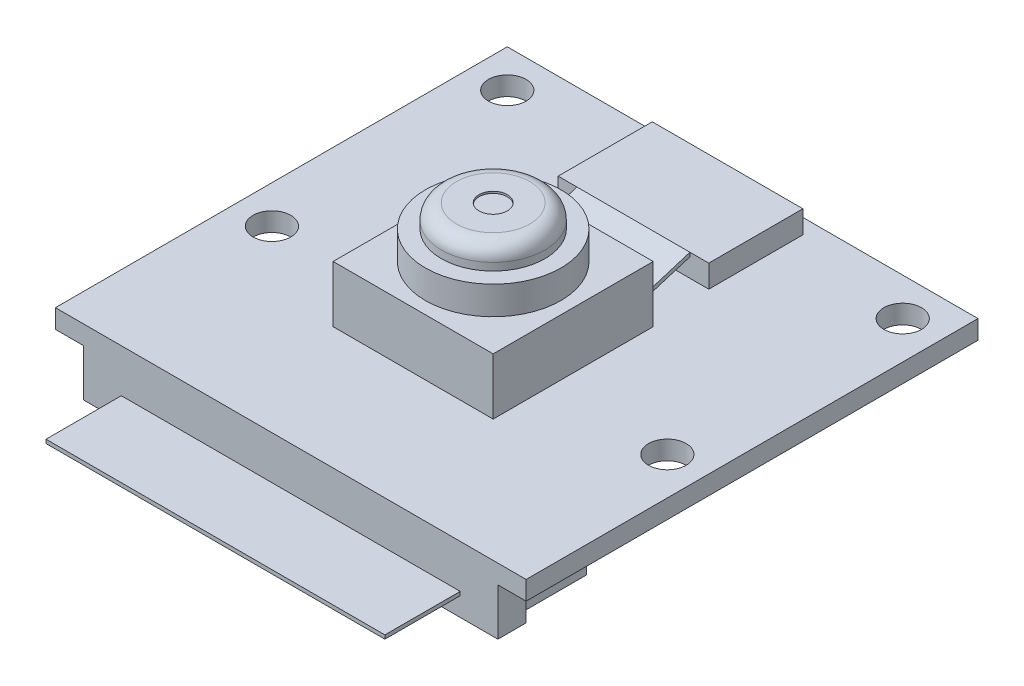
SolidWorks part; units mm, degrees
ref_plane "前视基准面" through (0, 0, 0) normal (0, 0, 1) x (1, 0, 0)
ref_plane "上视基准面" through (0, 0, 0) normal (0, 1, 0) x (1, 0, 0)
ref_plane "右视基准面" through (0, 0, 0) normal (1, 0, 0) x (0, 0, -1)
sketch "草图1" plane through (0, 0, 0) normal (0, 1, 0) x (1, 0, 0)
  line L1 (12.5, -12) -> (-12.5, -12)
  line L2 (12.5, -12) -> (12.5, 12)
  line L3 (12.5, 12) -> (-12.5, 12)
  line L4 (-12.5, -12) -> (-12.5, 12)
  line L5 (12.5, -12) -> (-12.5, 12) construction
  line L6 (12.5, 12) -> (-12.5, -12) construction
  point P0 (0, 0)
  dimension "D1" = 24
  dimension "D2" = 25
extrude "凸台-拉伸1" add sketch "草图1" along normal blind 1
sketch "草图2" plane through (0, 1, 0) normal (0, 1, 0) x (1, 0, 0)
  line L0 (0, 12) -> (0, -12) construction
  line L1 (12.5, 12) -> (-12.5, 12) construction
  line L2 (-12.5, -12) -> (12.5, -12) construction
  line L3 (-12.5, 0) -> (12.5, 0) construction
  line L4 (-12.5, 12) -> (-12.5, -12) construction
  line L5 (12.5, -12) -> (12.5, 12) construction
  circle A0 centre (-10.5, 10) radius 1
  circle A1 centre (-10.5, -2.5) radius 1
  circle A2 centre (10.5, -2.5) radius 1
  circle A3 centre (10.5, 10) radius 1
  dimension "D3" = 2
  dimension "D4" = 2
  dimension "D1" = 2
  dimension "D2" = 2
extrude "切除-拉伸1" cut sketch "草图2" against normal up to next
sketch "草图3" plane through (0, 1, 0) normal (0, 1, 0) x (1, 0, 0)
  line L0 (0, 12) -> (0, -12) construction
  line L1 (12.5, 12) -> (-12.5, 12) construction
  line L2 (-12.5, -12) -> (12.5, -12) construction
  line L4 (4.25, -5.5) -> (-4.25, -5.5)
  line L5 (4.25, -5.5) -> (4.25, 3)
  line L6 (4.25, 3) -> (-4.25, 3)
  line L7 (-4.25, -5.5) -> (-4.25, 3)
  line L8 (4.25, -5.5) -> (-4.25, 3) construction
  line L9 (4.25, 3) -> (-4.25, -5.5) construction
  point P6 (0, -1.25)
  dimension "D1" = 8.5
  dimension "D2" = 8.5
  dimension "D3" = 6.5
extrude "凸台-拉伸2" add sketch "草图3" along normal blind 3
sketch "草图4" plane through (0, 4, 0) normal (0, 1, 0) x (1, 0, 0)
  line L0 (-4.25, -1.25) -> (4.25, -1.25) construction
  line L1 (-4.25, 3) -> (-4.25, -5.5) construction
  line L2 (4.25, -5.5) -> (4.25, 3) construction
  line L3 (0, 3) -> (0, -5.5) construction
  line L4 (4.25, 3) -> (-4.25, 3) construction
  line L5 (-4.25, -5.5) -> (4.25, -5.5) construction
  circle A0 centre (0, -1.25) radius 3.6
  dimension "D1" = 7.2
extrude "凸台-拉伸3" add sketch "草图4" along normal blind 1.5
sketch "草图5" plane through (0, 5.5, 0) normal (0, 1, 0) x (1, 0, 0)
  line L0 (-4.25, -1.25) -> (4.25, -1.25) construction
  line L1 (-4.25, 3) -> (-4.25, -5.5) construction
  line L2 (4.25, -5.5) -> (4.25, 3) construction
  line L3 (0, 3) -> (0, -5.5) construction
  line L4 (4.25, 3) -> (-4.25, 3) construction
  line L5 (-4.25, -5.5) -> (4.25, -5.5) construction
  circle A0 centre (0, -1.25) radius 2.75
  dimension "D1" = 5.5
extrude "凸台-拉伸4" add sketch "草图5" along normal blind 1.2
fillet "圆角1" radius 0.8 1 edges at (0, 6.7, 4)
sketch "草图6" plane through (0, 6.7, 0) normal (0, 1, 0) x (1, 0, 0)
  line L4 (-4.25, 3) -> (-4.25, -5.5)
  line L5 (-4.25, -5.5) -> (4.25, -5.5)
  line L6 (4.25, -5.5) -> (4.25, 3)
  line L7 (4.25, 3) -> (-4.25, 3)
  line L8 (-4.25, 3) -> (-4.25, -5.5) construction
  line L9 (-4.25, -5.5) -> (4.25, -5.5) construction
  line L10 (4.25, -5.5) -> (4.25, 3) construction
  line L11 (4.25, 3) -> (-4.25, 3) construction
  circle A0 centre (0, -1.25) radius 0.75
  dimension "D2" = 1.5
  dimension "D1" = 0
extrude "切除-拉伸2" cut sketch "草图6" against normal blind 0.1
sketch "草图7" plane through (0, 1, 0) normal (0, 1, 0) x (1, 0, 0)
  line L1 (4, 6.2) -> (-4, 6.2)
  line L2 (4, 6.2) -> (4, 11.2)
  line L3 (4, 11.2) -> (-4, 11.2)
  line L4 (-4, 6.2) -> (-4, 11.2)
  line L5 (4, 6.2) -> (-4, 11.2) construction
  line L6 (4, 11.2) -> (-4, 6.2) construction
  line L10 (-12.5, 12) -> (-12.5, -12)
  line L11 (-12.5, -12) -> (12.5, -12)
  line L12 (12.5, -12) -> (12.5, 12)
  line L13 (12.5, 12) -> (-12.5, 12)
  line L14 (-12.5, 12) -> (-12.5, -12) construction
  line L15 (-12.5, -12) -> (12.5, -12) construction
  line L16 (12.5, -12) -> (12.5, 12) construction
  line L17 (12.5, 12) -> (-12.5, 12) construction
  point P0 (0, 8.7)
  point P7 (0, 0)
  point P9 (0, 12)
  dimension "D1" = 5
  dimension "D2" = 8
  dimension "D4" = 0.8
  dimension "D3" = 0
extrude "凸台-拉伸5" add sketch "草图7" along normal blind 1.2
sketch "草图8" plane through (0, 0, 0) normal (1, 0, 0) x (0, 0, -1)
  line L0 (3, 1.2094) -> (6.2, 2.2)
  line L1 (3, 4) -> (3, 1) construction
  line L2 (6.2, 2.2) -> (6.2, 1.9906)
  line L3 (6.2, 2.2) -> (6.2, 1) construction
  line L4 (6.2, 1.9906) -> (3, 1)
  line L5 (3, 1) -> (3, 1.2094)
  dimension "D1" = 0.2
extrude "凸台-拉伸6" add sketch "草图8" along normal blind 3 and the other way blind 3 separate body
sketch "草图9" plane through (0, 0, 0) normal (0, -1, 0) x (1, 0, 0)
  line L0 (-12.5, 12) -> (12.5, 12) construction
  line L1 (11, 10.5) -> (-11, 10.5)
  line L2 (11, 10.5) -> (11, 12)
  line L3 (11, 12) -> (-11, 12)
  line L4 (-11, 10.5) -> (-11, 12)
  line L5 (11, 10.5) -> (-11, 12) construction
  line L6 (11, 12) -> (-11, 10.5) construction
  point P0 (0, 11.25)
  point P7 (0, 0)
  dimension "D1" = 1.5
  dimension "D2" = 22
extrude "凸台-拉伸7" add sketch "草图9" along normal blind 2.5
sketch "草图12" plane through (0, 0, 0) normal (0, -1, 0) x (1, 0, 0)
  line L0 (-12.5, -12) -> (-12.5, 12) construction
  line L1 (-10.5, 10.5) -> (10.5, 10.5)
  line L2 (-10.5, 10.5) -> (-10.5, 6.8)
  line L3 (-10.5, 6.8) -> (10.5, 6.8)
  line L4 (10.5, 10.5) -> (10.5, 6.8)
  point P5 (0, 0)
  dimension "D1" = 21
  dimension "D2" = 3.7
  dimension "D3" = 2
extrude "凸台-拉伸8" add sketch "草图12" along normal blind 2.4
sketch "草图13" plane through (0, 0, 0) normal (1, 0, 0) x (0, 0, -1)
  line L0 (-6.8, -1.0088) -> (-6.1774, -0.1907)
  line L1 (-6.8, -2.4) -> (-6.8, 0) construction
  line L2 (-6.1774, -0.1907) -> (-4.9878, 0)
  line L3 (-12, 0) -> (12, 0) construction
  line L4 (-4.9878, 0) -> (-4.3247, 0)
  line L5 (-4.3247, 0) -> (-6.1264, -0.2889)
  line L6 (-6.1264, -0.2889) -> (-6.8, -1.1739)
  line L7 (-6.8, -2.4) -> (-6.8, -1.1739)
  line L11 (-6.8, 0) -> (-10.5, 0)
  line L12 (-10.5, 0) -> (-10.5, -2.4)
  line L13 (-10.5, -2.4) -> (-6.8, -2.4)
  line L14 (-6.8, -2.4) -> (-6.8, 0)
  line L15 (-6.8, 0) -> (-10.5, 0)
  line L16 (-10.5, 0) -> (-10.5, -2.4)
  line L17 (-10.5, -2.4) -> (-6.8, -2.4)
  line L18 (-6.8, -1.0088) -> (-6.8, 0)
  point P7 (-6.1774, -0.1907)
  point P11 (-4.9878, 0)
  dimension "D1" = 0.105
  dimension "D2" = 0.1
  dimension "D3" = 0
extrude "凸台-拉伸9" add sketch "草图13" along normal blind 0.1 and the other way blind 0.1
pattern_linear "阵列(线性)1" count 8 spacing 1.2 along (1, 0, 0) count 8 spacing 1.2 along (-1, 0, 0) of "凸台-拉伸9"
sketch "草图14" plane through (0, 0, 0) normal (0, -1, 0) x (1, 0, 0)
  line L1 (8.8483, -2.2) -> (5.8483, -2.2)
  line L2 (8.8483, -2.2) -> (8.8483, -0.7)
  line L3 (8.8483, -0.7) -> (5.8483, -0.7)
  line L4 (5.8483, -2.2) -> (5.8483, -0.7)
  dimension "D1" = 1.5
  dimension "D2" = 3
extrude "凸台-拉伸10" add sketch "草图14" along normal blind 1
ref_plane "基准面1" through (7.3483, 0, 0) normal (1, 0, 0) x (0, 0, -1)
sketch "草图15" plane through (7.3483, 0, 0) normal (1, 0, 0) x (0, 0, -1)
  line L0 (0.7, -0.5) -> (0.4948, -0.1663)
  line L1 (0.7, -1) -> (0.7, 0) construction
  line L2 (0.4948, -0.1663) -> (-0.1865, 0)
  line L3 (-12, 0) -> (12, 0) construction
  line L4 (0.5585, -0.0789) -> (0.2352, 0)
  line L5 (0.2352, 0) -> (-0.1865, 0)
  line L6 (0.5585, -0.0789) -> (0.7, -0.309)
  line L7 (0.7, 0) -> (0.7, -0.309)
  line L11 (2.2, 0) -> (0.7, 0)
  line L12 (0.7, 0) -> (0.7, -1)
  line L13 (0.7, -1) -> (2.2, -1)
  line L14 (2.2, -1) -> (2.2, 0)
  line L15 (2.2, 0) -> (0.7, 0)
  line L16 (0.7, -0.5) -> (0.7, -1)
  line L17 (0.7, -1) -> (2.2, -1)
  line L18 (2.2, -1) -> (2.2, 0)
  point P4 (0.5683, -0.0945)
  point P8 (-0.1865, 0)
  point P11 (0.4948, -0.1663)
  dimension "D1" = 0.1
  dimension "D2" = 0.1
  dimension "D3" = 0
extrude "凸台-拉伸11" add sketch "草图15" along normal blind 0.15 and the other way blind 0.15
pattern_linear "阵列(线性)2" count 2 spacing 1 along (-1, 0, 0) count 2 spacing 1 along (1, 0, 0) of "凸台-拉伸11"
ref_plane "基准面2" through (0, 0, -1.45) normal (0, 0, 1) x (1, 0, 0)
mirror "镜向1" about plane through (0, 0, -1.45) normal (0, 0, 1) of "阵列(线性)2", "凸台-拉伸11"
pattern_linear "阵列(线性)3" count 3 spacing 5 along (-1, 0, 0) of "镜向1", "阵列(线性)2", "凸台-拉伸11", "凸台-拉伸10"
sketch "草图16" plane through (0, 0, 0) normal (0, -1, 0) x (1, 0, 0)
  line L1 (-6.1142, -8.4922) -> (-8.6142, -8.4922)
  line L2 (-6.1142, -8.4922) -> (-6.1142, -5.4922)
  line L3 (-6.1142, -5.4922) -> (-8.6142, -5.4922)
  line L4 (-8.6142, -8.4922) -> (-8.6142, -5.4922)
  point P4 (-8.6142, -6.9922)
  dimension "D1" = 3
  dimension "D2" = 2.5
extrude "凸台-拉伸12" add sketch "草图16" along normal blind 1.2
fillet "圆角2" radius 0.2 52 edges at (2.3483, -0.1663, -0.4948) (2.3483, -0.0789, -0.5585) (-2.6517, -0.1663, -0.4948) (-2.6517, -0.0789, -0.5585) (3.3483, -0.1663, -0.4948) (3.3483, -0.0789, -0.5585) (1.3483, -0.1663, -0.4948) (1.3483, -0.0789, -0.5585) (-1.6517, -0.1663, -0.4948) (-1.6517, -0.0789, -0.5585) (-3.6517, -0.1663, -0.4948) (-3.6517, -0.0789, -0.5585) (2.3483, -0.0789, -2.3414) (2.3483, -0.1663, -2.4051) (3.3483, -0.0789, -2.3414) (3.3483, -0.1663, -2.4051) (1.3483, -0.0789, -2.3414) (1.3483, -0.1663, -2.4051) (-2.6517, -0.0789, -2.3414) (-2.6517, -0.1663, -2.4051) (-1.6517, -0.0789, -2.3414) (-1.6517, -0.1663, -2.4051) (-3.6517, -0.0789, -2.3414) (-3.6517, -0.1663, -2.4051) (-6.1142, -1.2, -6.9922) (-7.3642, -1.2, -5.4922) (-8.6142, -1.2, -6.9922) (-7.3642, -1.2, -8.4922) (8.8483, -1, -1.45) (7.3483, -1, -0.7) (5.8483, -1, -1.45) (7.3483, -1, -2.2) (7.3483, -0.1663, -0.4948) (7.3483, -0.0789, -0.5585) (8.3483, -0.1663, -0.4948) (8.3483, -0.0789, -0.5585) (6.3483, -0.1663, -0.4948) (6.3483, -0.0789, -0.5585) (7.3483, -0.0789, -2.3414) (7.3483, -0.1663, -2.4051) (8.3483, -0.0789, -2.3414) (8.3483, -0.1663, -2.4051) (6.3483, -0.0789, -2.3414) (6.3483, -0.1663, -2.4051) (3.8483, -1, -1.45) (2.3483, -1, -0.7) (0.8483, -1, -1.45) (2.3483, -1, -2.2) (-1.1517, -1, -1.45) (-2.6517, -1, -0.7) (-4.1517, -1, -1.45) (-2.6517, -1, -2.2)
sketch "草图17" plane through (0, 0, 12) normal (0, 0, 1) x (1, 0, 0)
  line L0 (-11, -2.5) -> (-11, 0) construction
  line L1 (-9, -1.3) -> (9, -1.3)
  line L2 (-9, -1.3) -> (-9, -1.5)
  line L3 (-9, -1.5) -> (9, -1.5)
  line L4 (9, -1.3) -> (9, -1.5)
  line L5 (11, -2.5) -> (11, 0) construction
  line L6 (11, -2.5) -> (-11, -2.5) construction
  dimension "D1" = 2
  dimension "D2" = 2
  dimension "D3" = 1
  dimension "D4" = 0.2
extrude "凸台-拉伸13" add sketch "草图17" along normal blind 4
